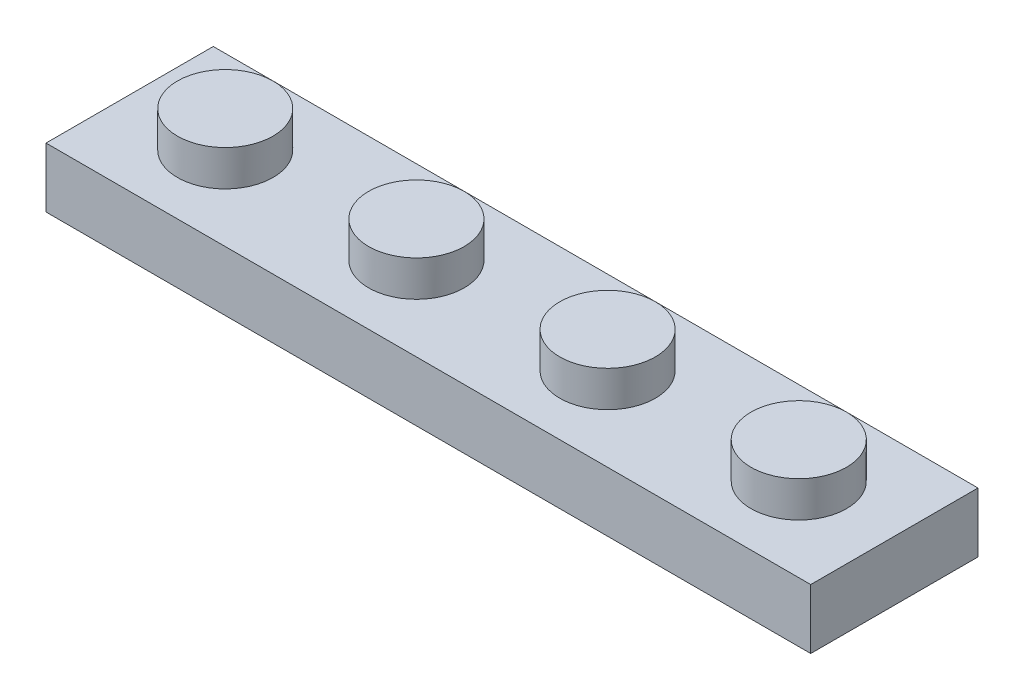
SolidWorks part; units mm, degrees
material "ABS"
ref_plane "Front Plane" through (0, 0, 0) normal (0, 0, 1) x (1, 0, 0)
ref_plane "Top Plane" through (0, 0, 0) normal (0, 1, 0) x (1, 0, 0)
ref_plane "Right Plane" through (0, 0, 0) normal (1, 0, 0) x (0, 0, -1)
sketch "Sketch1" plane through (0, 0, 0) normal (0, 0, 1) x (1, 0, 0)
  line L0 (-20.32, 0) -> (20.32, 0)
  line L1 (20.32, 0) -> (20.32, -3.175)
  line L2 (20.32, -3.175) -> (-20.32, -3.175)
  line L3 (-20.32, -3.175) -> (-20.32, 0)
  point P3 (0, -3.175)
  dimension "D1" = 40.64
  dimension "D2" = 3.175
extrude "Boss-Extrude1" add sketch "Sketch1" along normal mid plane 8.89
sketch "Sketch2" plane through (0, 0, 0) normal (0, 1, 0) x (1, 0, 0)
  line L0 (-20.32, 0) -> (0, 0) construction
  line L1 (-20.32, -4.445) -> (-20.32, 4.445) construction
  line L2 (-20.32, -4.445) -> (-10.16, 4.445) construction
  line L3 (20.32, 4.445) -> (-20.32, 4.445) construction
  line L4 (-10.16, 4.445) -> (0, -4.445) construction
  line L5 (20.32, -4.445) -> (-20.32, -4.445) construction
  line L6 (0, -4.445) -> (0, 4.445) construction
  circle A0 centre (-15.24, 0) radius 2.54
  circle A1 centre (-5.08, 0) radius 2.54
  circle A2 centre (5.08, 0) radius 2.54
  circle A3 centre (15.24, 0) radius 2.54
  dimension "D1" = 5.08
  dimension "D2" = 5.08
extrude "Boss-Extrude2" add sketch "Sketch2" along normal blind 1.905
sketch "Sketch3" plane through (0, -3.175, 0) normal (0, -1, 0) x (1, 0, 0)
  line L0 (-19.05, 2.54) -> (-19.05, -2.54)
  line L1 (-19.05, -2.54) -> (19.05, -2.54)
  line L2 (19.05, -2.54) -> (19.05, 2.54)
  line L3 (19.05, 2.54) -> (-19.05, 2.54)
  line L4 (-20.32, 4.445) -> (-20.32, -4.445) construction
  line L5 (20.32, 4.445) -> (20.32, -4.445) construction
  line L6 (-20.32, -4.445) -> (20.32, -4.445) construction
  line L7 (-20.32, 4.445) -> (20.32, 4.445) construction
  dimension "D1" = 1.27
  dimension "D2" = 1.27
  dimension "D3" = 1.905
  dimension "D4" = 1.905
extrude "Cut-Extrude1" cut sketch "Sketch3" against normal blind 1.905
sketch "Sketch4" plane through (0, -1.27, 0) normal (0, -1, 0) x (1, 0, 0)
  line L0 (-20.32, 0) -> (0, 0) construction
  line L1 (-20.32, 4.445) -> (-20.32, -4.445) construction
  line L2 (-20.32, -4.445) -> (-10.16, 4.445) construction
  line L3 (-20.32, 4.445) -> (20.32, 4.445) construction
  line L4 (-10.16, 4.445) -> (0, -4.445) construction
  line L5 (-20.32, -4.445) -> (20.32, -4.445) construction
  line L6 (0, -4.445) -> (0, 4.445) construction
  circle A0 centre (-15.24, 0) radius 1.905
  circle A1 centre (-5.08, 0) radius 1.905
  circle A2 centre (5.08, 0) radius 1.905
  circle A3 centre (15.24, 0) radius 1.905
  dimension "D1" = 3.81
  dimension "D2" = 3.81
extrude "Cut-Extrude2" cut sketch "Sketch4" against normal blind 2.54
sketch "Sketch5" plane through (0, -1.27, 0) normal (0, -1, 0) x (1, 0, 0)
  line L0 (-20.32, 0) -> (0, 0) construction
  line L1 (-20.32, 4.445) -> (-20.32, -4.445) construction
  line L2 (0, 0) -> (0, 4.8807) construction
  line L3 (-5.08, 0) -> (-5.08, 6.1998) construction
  circle A0 centre (-10.16, 0) radius 1.905
  circle A1 centre (-10.16, 0) radius 0.9525
  circle A2 centre (10.16, 0) radius 0.9525
  circle A3 centre (10.16, 0) radius 1.905
  circle A4 centre (0, 0) radius 0.9525
  circle A5 centre (0, 0) radius 1.905
  dimension "D1" = 3.81
  dimension "D2" = 1.905
extrude "Boss-Extrude3" add sketch "Sketch5" along normal up to surface (1.905 mm away) up to face at (0, -3.175, 0)
